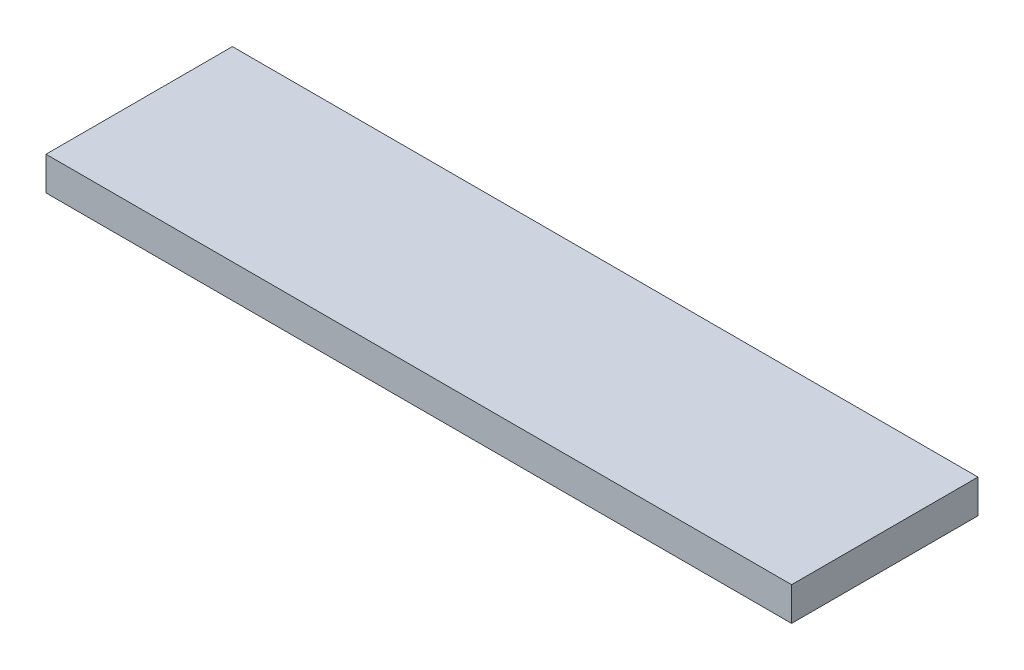
SolidWorks part; units mm, degrees
ref_plane "Front Plane" through (0, 0, 0) normal (0, 0, 1) x (1, 0, 0)
ref_plane "Top Plane" through (0, 0, 0) normal (0, 1, 0) x (1, 0, 0)
ref_plane "Right Plane" through (0, 0, 0) normal (1, 0, 0) x (0, 0, -1)
sketch "Sketch1" plane through (0, 0, 0) normal (0, 1, 0) x (1, 0, 0)
  line L1 (0, 0) -> (400, 0)
  line L2 (0, 0) -> (0, 100)
  line L3 (0, 100) -> (400, 100)
  line L4 (400, 0) -> (400, 100)
  dimension "D1" = 100
  dimension "D2" = 400
extrude "Boss-Extrude1" add sketch "Sketch1" along normal blind 18
